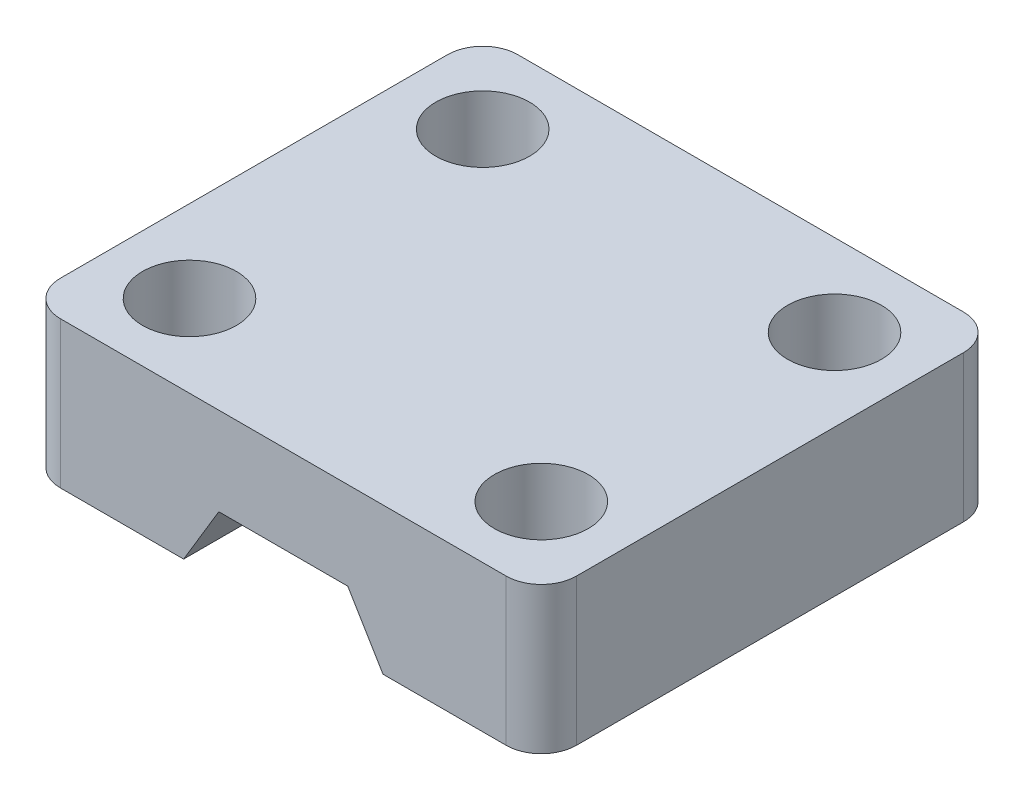
SolidWorks part; units mm, degrees
ref_plane "Front Plane" through (0, 0, 0) normal (0, 0, 1) x (1, 0, 0)
ref_plane "Top Plane" through (0, 0, 0) normal (0, 1, 0) x (1, 0, 0)
ref_plane "Right Plane" through (0, 0, 0) normal (1, 0, 0) x (0, 0, -1)
sketch "Sketch1" plane through (0, 0, 0) normal (0, 0, 1) x (1, 0, 0)
  line L0 (13.5, -12.5) -> (16.5, -7.5)
  line L1 (0, 0) -> (44, 0)
  line L2 (0, 0) -> (0, -12.5)
  line L3 (0, -12.5) -> (13.5, -12.5)
  line L4 (44, 0) -> (44, -12.5)
  line L5 (16.5, -7.5) -> (27.5, -7.5)
  line L6 (27.5, -7.5) -> (30.5, -12.5)
  line L7 (30.5, -12.5) -> (44, -12.5)
  point P9 (22, -7.5)
  point P11 (22, 0)
  dimension "D1" = 17
  dimension "D2" = 11
  dimension "D3" = 5
  dimension "D4" = 8.5
  dimension "D5" = 12.5
  dimension "D6" = 44
extrude "Boss-Extrude1" add sketch "Sketch1" along normal blind 39
sketch "Sketch2" plane through (0, 0, 0) normal (0, 1, 0) x (1, 0, 0)
  line L0 (44, 0) -> (0, 0) construction
  line L2 (44, -39) -> (44, 0) construction
  circle A0 centre (7, -7) radius 4
  circle A1 centre (37, -7) radius 4
  circle A2 centre (37, -32) radius 4
  circle A3 centre (7, -32) radius 4
  point P15 (22, 0)
  point P21 (44, -19.5)
  dimension "D3" = 8
  dimension "D1" = 30
  dimension "D2" = 25
  dimension "D4" = 15
  dimension "D5" = 12.5
extrude "Cut-Extrude1" cut sketch "Sketch2" against normal through all
fillet "Fillet1" radius 3 4 edges at (0, -6.25, 0) (44, -6.25, 0) (44, -6.25, 39) (0, -6.25, 39)
